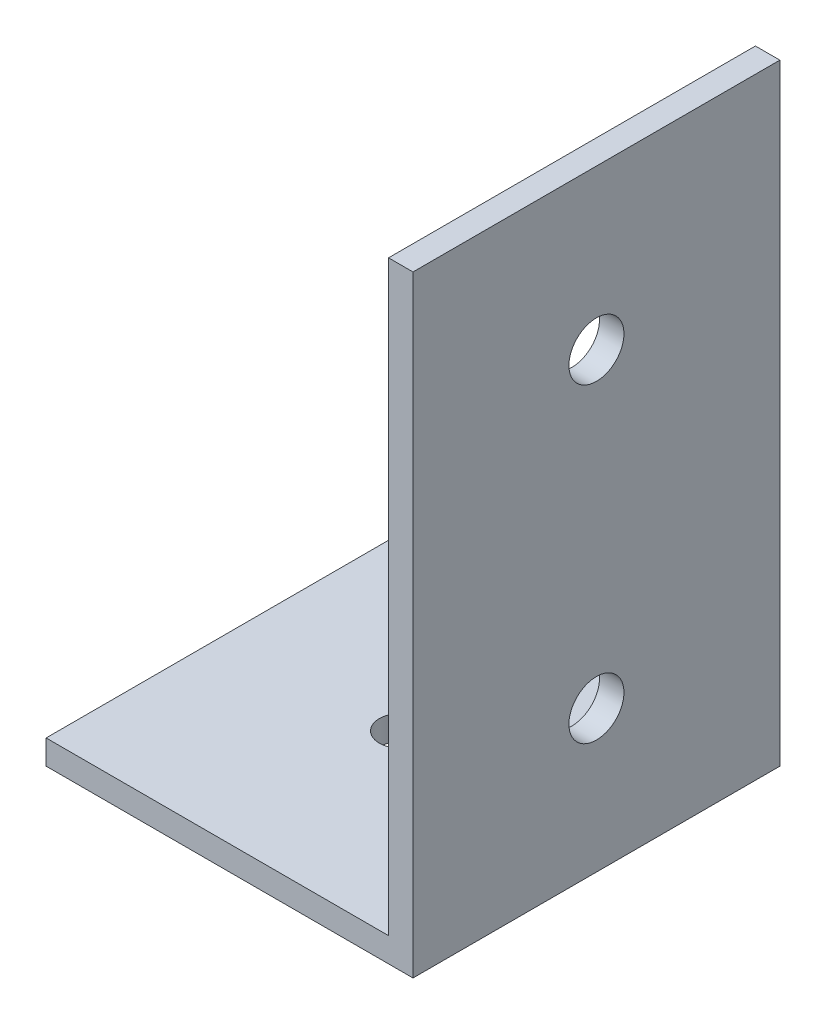
SolidWorks part; units mm, degrees
ref_plane "Piano frontale" through (0, 0, 0) normal (0, 0, 1) x (1, 0, 0)
ref_plane "Piano superiore" through (0, 0, 0) normal (0, 1, 0) x (1, 0, 0)
ref_plane "Piano destro" through (0, 0, 0) normal (1, 0, 0) x (0, 0, -1)
sketch "Schizzo1" plane through (0, 0, 0) normal (0, 0, 1) x (1, 0, 0)
  line L0 (0, 0) -> (-30, 0)
  line L1 (-30, 0) -> (-30, 2)
  line L2 (-30, 2) -> (-2, 2)
  line L3 (-2, 2) -> (-2, 50)
  line L4 (-2, 50) -> (0, 50)
  line L5 (0, 50) -> (0, 0)
  dimension "D1" = 50
  dimension "D2" = 30
  dimension "D3" = 2
extrude "Estrusione-Estrusione1" add sketch "Schizzo1" along normal blind 30
sketch "Schizzo2" plane through (-2, 0, 0) normal (-1, 0, 0) x (0, 0, 1)
  line L0 (30, 0) -> (0, 0) construction
  line L1 (15, 39.25) -> (15, 5.7333) construction
  line L2 (30, 50) -> (30, 2) construction
  line L3 (0, 50) -> (0, 2) construction
  circle A0 centre (15, 37) radius 2.25
  circle A1 centre (15, 11.6) radius 2.25
  dimension "D2" = 4.5
  dimension "D4" = 4.5
  dimension "D1" = 37
  dimension "D3" = 11.6
extrude "Taglio-Estrusione1" cut sketch "Schizzo2" against normal through all
sketch "Schizzo3" plane through (0, 2, 0) normal (0, 1, 0) x (1, 0, 0)
  line L0 (-30, -15) -> (-2, -15) construction
  line L1 (-30, -30) -> (-30, 0) construction
  line L2 (-2, -30) -> (-2, 0) construction
  line L3 (-16, 0) -> (-16, -30) construction
  line L4 (-2, 0) -> (-30, 0) construction
  line L5 (-2, -30) -> (-30, -30) construction
  circle A0 centre (-16, -15) radius 1.75
  dimension "D1" = 3.5
extrude "Taglio-Estrusione2" cut sketch "Schizzo3" against normal through all
